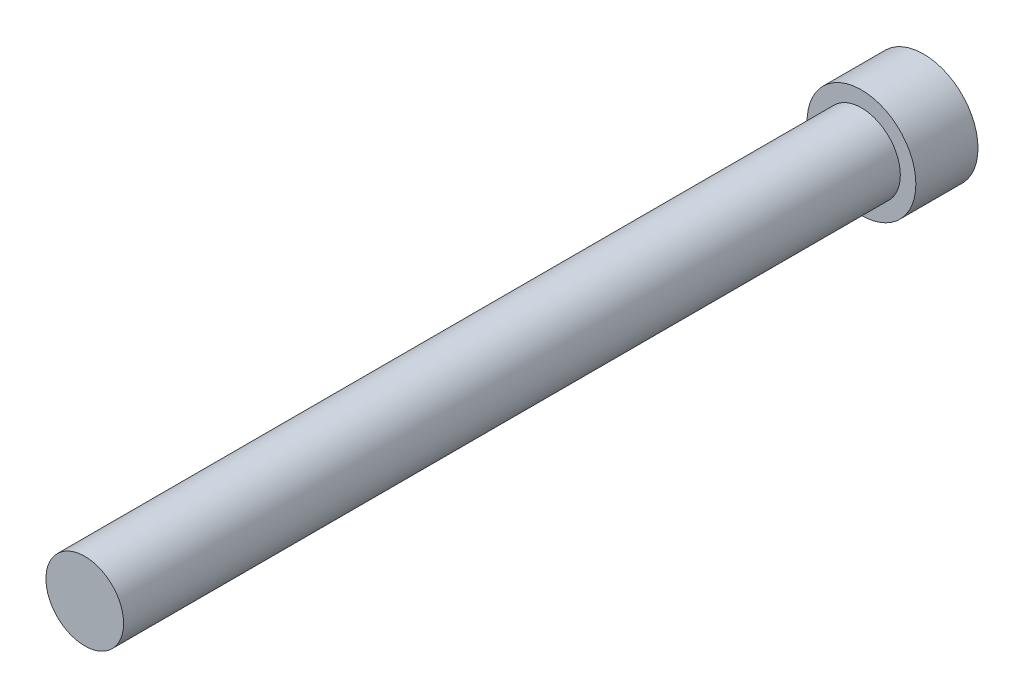
SolidWorks part; units mm, degrees
ref_plane "Front Plane" through (0, 0, 0) normal (0, 0, 1) x (1, 0, 0)
ref_plane "Top Plane" through (0, 0, 0) normal (0, 1, 0) x (1, 0, 0)
ref_plane "Right Plane" through (0, 0, 0) normal (1, 0, 0) x (0, 0, -1)
sketch "Sketch1" plane through (0, 0, 0) normal (0, 0, 1) x (1, 0, 0)
  circle A0 centre (0, 0) radius 4.445
extrude "Extrude1" add sketch "Sketch1" along normal blind 68.58
sketch "Sketch2" plane through (0, 0, 68.58) normal (0, 0, 1) x (1, 0, 0)
  circle A0 centre (0, 0) radius 3.175
extrude "Extrude2" cut sketch "Sketch2" against normal blind 63.5 flip side to cut
